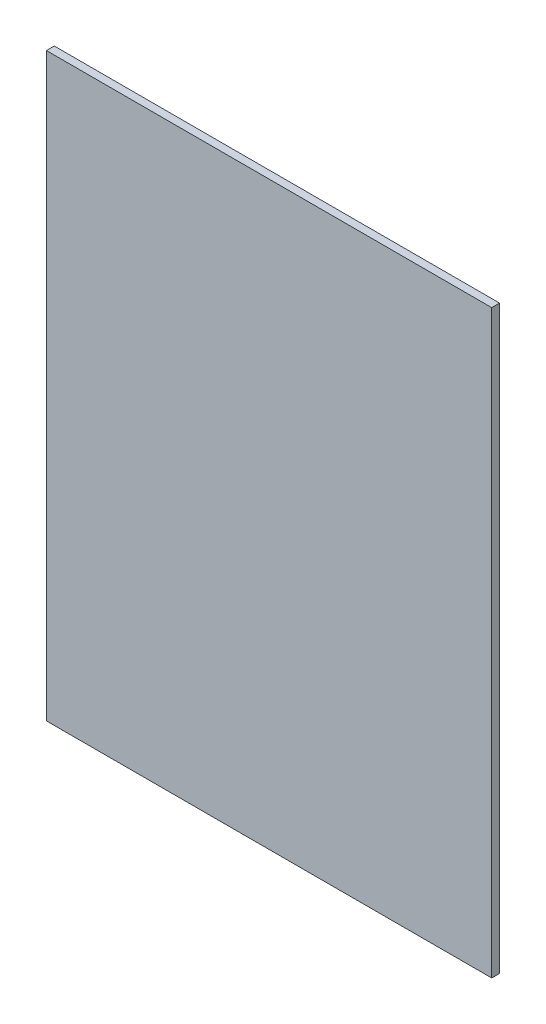
SolidWorks part; units mm, degrees
ref_plane "Front Plane" through (0, 0, 0) normal (0, 0, 1) x (1, 0, 0)
ref_plane "Top Plane" through (0, 0, 0) normal (0, 1, 0) x (1, 0, 0)
ref_plane "Right Plane" through (0, 0, 0) normal (1, 0, 0) x (0, 0, -1)
sketch "Sketch1" plane through (0, 0, 0) normal (0, 0, 1) x (1, 0, 0)
  line L1 (-180.213, 234.95) -> (180.213, 234.95)
  line L2 (-180.213, 234.95) -> (-180.213, -234.95)
  line L3 (-180.213, -234.95) -> (180.213, -234.95)
  line L4 (180.213, 234.95) -> (180.213, -234.95)
  line L5 (-180.213, 234.95) -> (180.213, -234.95) construction
  line L6 (-180.213, -234.95) -> (180.213, 234.95) construction
  point P0 (0, 0)
  dimension "D1" = 360.426
  dimension "D2" = 469.9
extrude "Boss-Extrude1" add sketch "Sketch1" along normal blind 6.35
